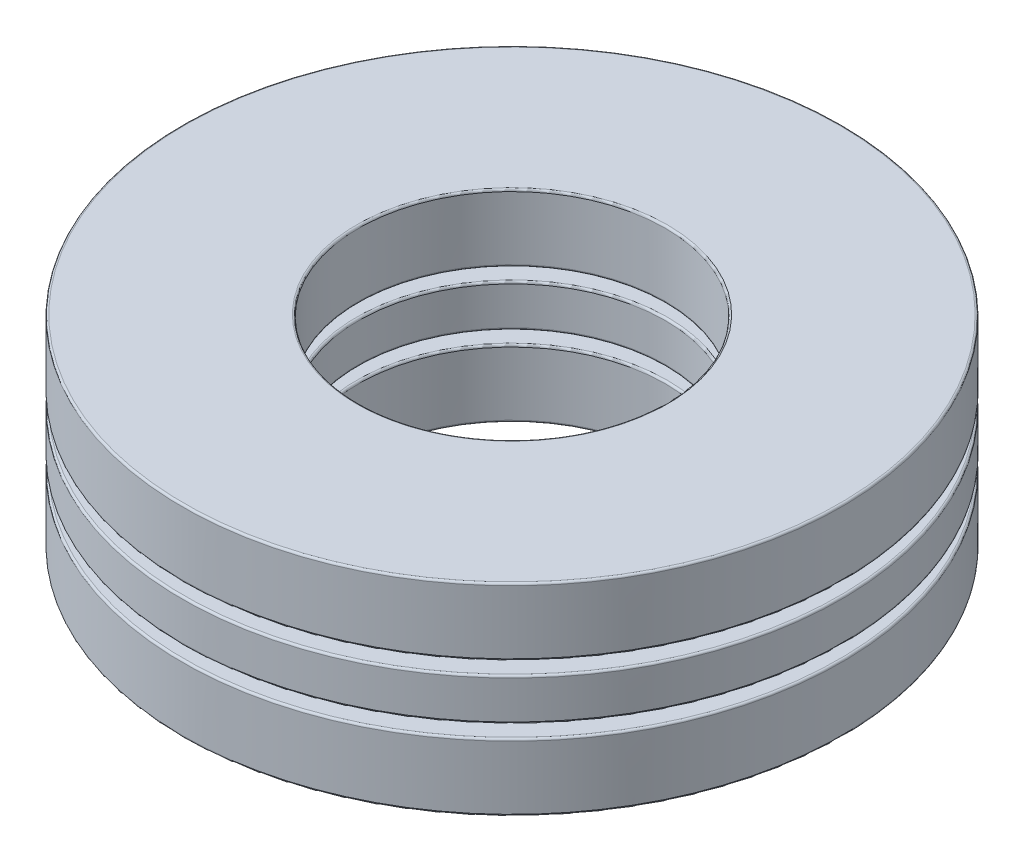
SolidWorks part; units mm, degrees
ref_plane "Front Plane" through (0, 0, 0) normal (0, 0, 1) x (1, 0, 0)
ref_plane "Top Plane" through (0, 0, 0) normal (0, 1, 0) x (1, 0, 0)
ref_plane "Right Plane" through (0, 0, 0) normal (1, 0, 0) x (0, 0, -1)
sketch "Sketch1" plane through (0, 0, 0) normal (1, 0, 0) x (0, 0, -1)
  line L0 (-10.3187, 0) -> (10.3187, 0) construction
  line L1 (0, -3.1623) -> (0, 3.1623) construction
  line L2 (-10.3187, 0.6588) -> (-4.8006, 0.6588)
  line L3 (-10.3187, 0.6588) -> (-10.3187, -0.6588)
  line L4 (-10.3187, -0.6588) -> (-4.8006, -0.6588)
  line L5 (-4.8006, 0.6588) -> (-4.8006, -0.6588)
  line L6 (-7.5597, 1.0541) -> (-7.5597, -1.0541) construction
  circle A0 centre (-7.5597, 0) radius 1.0541 construction
  point P13 (-7.5597, 0.6588)
  dimension "OD" = 20.6375
  dimension "Shaft Dia" = 9.6012
  dimension "Th" = 6.3246
  dimension "D1" = 2.1082
  dimension "D2" = 1.3176
revolve "Revolve1" add sketch "Sketch1" angle 360 about L1
sketch "Sketch3" plane through (0, 0, 0) normal (1, 0, 0) x (0, 0, -1)
  line L0 (-7.5597, 1.0541) -> (-7.5597, -1.0541)
  arc A0 (-7.5597, 1.0541) -> (-7.5597, -1.0541) centre (-7.5597, 0) ccw
  circle A1 centre (-7.5597, 0) radius 1.0541 construction
revolve "Cut-Revolve1" cut sketch "Sketch3" angle 360 about L0
sketch "Sketch2" plane through (0, 0, 0) normal (1, 0, 0) x (0, 0, -1)
  line L0 (-7.5597, 1.0541) -> (-7.5597, -1.0541)
  arc A0 (-7.5597, 1.0541) -> (-7.5597, -1.0541) centre (-7.5597, 0) ccw
  circle A2 centre (-7.5597, 0) radius 1.0541 construction
revolve "Revolve2" add sketch "Sketch2" angle 360 about L0
ref_axis "Axis1" through (0, 3.1623, 0) along (0, -1, 0)
pattern_circular "CirPattern1" count 4 every 90 about axis through (0, 3.1623, 0) along (0, -1, 0) of bodies 187
pattern_circular "CirPattern2" count 4 every 90 about axis through (0, 0, 0) along (0, 1, 0) of "Cut-Revolve1"
sketch "Sketch4" plane through (0, 0, 0) normal (1, 0, 0) x (0, 0, -1)
  line L0 (-10.3187, 0.6588) -> (-10.3187, -0.6588) construction
  line L1 (-10.3187, 1.0541) -> (-4.8006, 1.0541)
  line L2 (-10.3187, 1.0541) -> (-10.3187, 3.1623)
  line L3 (-10.3187, 3.1623) -> (-4.8006, 3.1623)
  line L4 (-4.8006, 1.0541) -> (-4.8006, 3.1623)
  line L5 (-10.3187, -3.1623) -> (-4.8006, -3.1623)
  line L6 (-10.3187, -3.1623) -> (-10.3187, -1.0541)
  line L7 (-10.3187, -1.0541) -> (-4.8006, -1.0541)
  line L8 (-4.8006, -3.1623) -> (-4.8006, -1.0541)
  line L9 (-7.5597, 1.0541) -> (-7.5597, -1.0541) construction
  line L10 (-4.8006, 0.6588) -> (-4.8006, -0.6588) construction
  line L11 (0, 0) -> (-10.3187, 0) construction
  line L12 (-10.3187, 0) -> (10.3187, 0) construction
  dimension "Ht" = 6.3246
revolve "Revolve3" add sketch "Sketch4" angle 360 about L1
fillet "Fillet1" radius 0.0632 4 edges at (0, 1.0541, -4.8006) (0, 3.1623, -4.8006) (0, 1.0541, -10.3187) (0, 3.1623, -10.3187)
fillet "Fillet2" radius 0.0632 4 edges at (0, -0.6588, -4.8006) (0, 0.6588, -4.8006) (0, -0.6588, -10.3187) (0, 0.6588, -10.3187)
fillet "Fillet3" radius 0.0632 4 edges at (0, -3.1623, -4.8006) (0, -1.0541, -4.8006) (0, -3.1623, -10.3187) (0, -1.0541, -10.3187)
equation "\"D1@Sketch1\" = \"Th@Sketch1\"/3"
equation "\"D2@Sketch1\" = \"D1@Sketch1\"*.625"
equation "\"Balls@CirPattern1\" = \"OD@Sketch1\"*5"
equation "\"Angle@CirPattern1\" = 360/\"Balls@CirPattern1\""
equation "\"D1@CirPattern2\" = \"Balls@CirPattern1\""
equation "\"D2@CirPattern2\" = \"Angle@CirPattern1\""
equation "\"D1@Fillet1\" = \"Th@Sketch1\"*.01"
equation "\"D1@Fillet2\" = \"D1@Fillet1\""
equation "\"D1@Fillet3\" = \"D1@Fillet1\""
